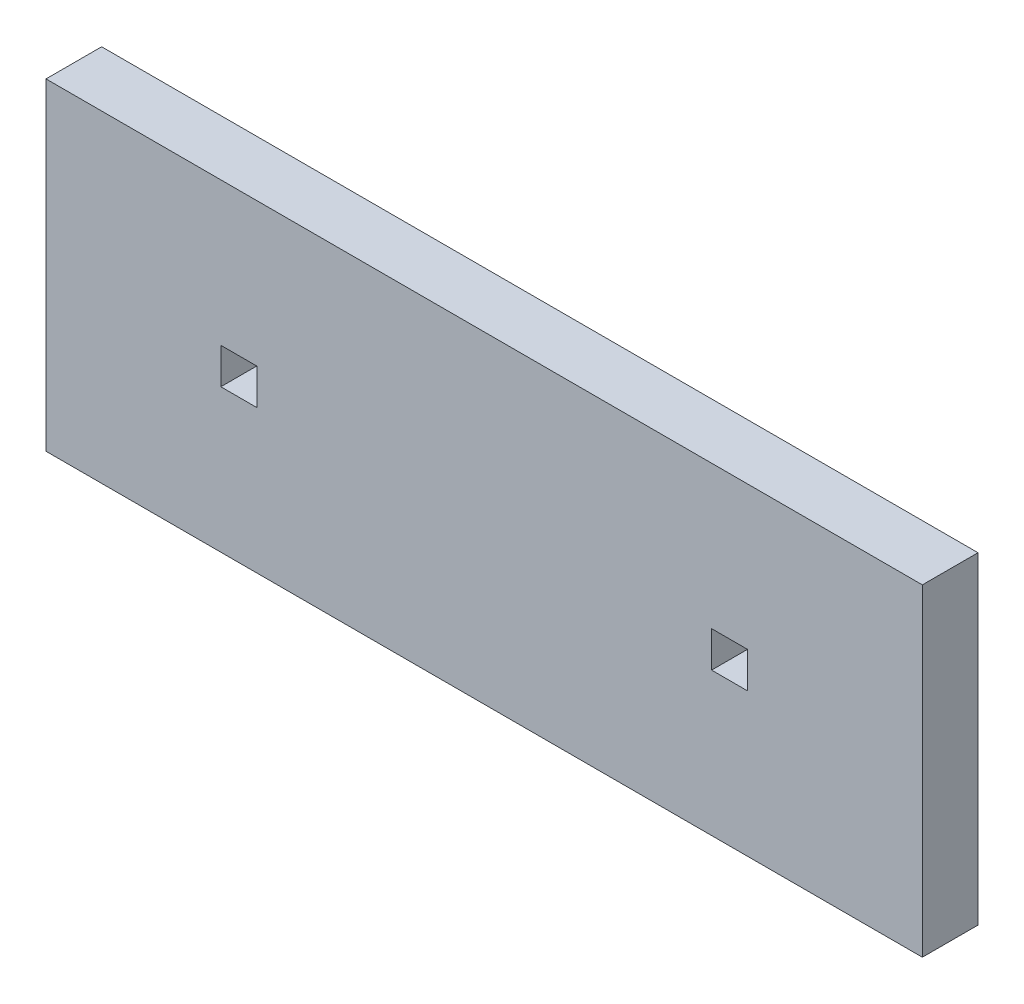
SolidWorks part; units mm, degrees
material "Acrylic (Medium-high impact)"
ref_plane "Front Plane" through (0, 0, 0) normal (0, 0, 1) x (1, 0, 0)
ref_plane "Top Plane" through (0, 0, 0) normal (0, 1, 0) x (1, 0, 0)
ref_plane "Right Plane" through (0, 0, 0) normal (1, 0, 0) x (0, 0, -1)
sketch "Sketch2" plane through (0, 0, 0) normal (0, 0, 1) x (1, 0, 0)
  line L0 (-12.975, -1.5875) -> (12.975, -1.5875) construction
  line L1 (25, -10.7875) -> (-25, -10.7875)
  line L2 (25, -10.7875) -> (25, 10.7875)
  line L3 (25, 10.7875) -> (-25, 10.7875)
  line L4 (-25, -10.7875) -> (-25, 10.7875)
  line L5 (25, -10.7875) -> (-25, 10.7875) construction
  line L6 (25, 10.7875) -> (-25, -10.7875) construction
  line L7 (-15.025, -0.5625) -> (-12.975, -0.5625)
  line L8 (-15.025, -0.5625) -> (-15.025, -2.6125)
  line L9 (-15.025, -2.6125) -> (-12.975, -2.6125)
  line L10 (-12.975, -0.5625) -> (-12.975, -2.6125)
  line L11 (15.025, -2.6125) -> (12.975, -2.6125)
  line L12 (15.025, -2.6125) -> (15.025, -0.5625)
  line L13 (15.025, -0.5625) -> (12.975, -0.5625)
  line L14 (12.975, -2.6125) -> (12.975, -0.5625)
  line L15 (-18, 10.7875) -> (-18, -10.7875) construction
  line L16 (0, -1.6485) -> (0, 1.6485) construction
  line L17 (22.5, 10.7875) -> (20.5, 10.7875)
  line L22 (-25, 10.7875) -> (-18, 10.7875)
  line L23 (-25, 10.7875) -> (-25, 7.6125)
  line L24 (-25, 7.6125) -> (-18, 7.6125)
  line L25 (-18, 10.7875) -> (-18, 7.6125)
  line L26 (-22.5, 7.6125) -> (-20.5, 7.6125)
  line L27 (-22.5, 7.6125) -> (-22.5, 10.7875)
  line L28 (-22.5, 10.7875) -> (-20.5, 10.7875)
  line L29 (-20.5, 7.6125) -> (-20.5, 10.7875)
  line L30 (20.5, 7.6125) -> (20.5, 10.7875)
  line L31 (22.5, 7.6125) -> (20.5, 7.6125)
  line L32 (22.5, 7.6125) -> (22.5, 10.7875)
  line L33 (25, 7.6125) -> (18, 7.6125)
  line L34 (18, 10.7875) -> (18, 7.6125)
  line L35 (25, 10.7875) -> (18, 10.7875)
  line L36 (25, 10.7875) -> (25, 7.6125)
  line L42 (-18, 10.7875) -> (18, 10.7875)
  line L43 (-18, 10.7875) -> (-18, 7.6125)
  line L44 (-18, 7.6125) -> (18, 7.6125)
  line L45 (18, 10.7875) -> (18, 7.6125)
  line L46 (-25, -1) -> (-28.175, -1)
  line L47 (-25, -1) -> (-25, 1)
  line L48 (-25, 1) -> (-28.175, 1)
  line L49 (-28.175, -1) -> (-28.175, 1)
  line L50 (25, -1) -> (28.175, -1)
  line L51 (25, -1) -> (25, 1)
  line L52 (25, 1) -> (28.175, 1)
  line L53 (28.175, -1) -> (28.175, 1)
  point P0 (0, 0)
  point P16 (0, -1.5875)
  point P29 (-21.5, 7.6125)
  point P30 (-21.5, 7.6125)
  point P32 (-22.5, 9.2)
  point P40 (-14, -0.5625)
  point P41 (14, -0.5625)
  point P42 (-15.025, -1.5875)
  point P49 (28.175, 0)
  point P50 (-28.175, 0)
  dimension "D1" = 2.05
  dimension "D3" = 50
  dimension "D6" = 7
  dimension "D7" = 2
  dimension "D8" = 3.175
  dimension "D4" = 28
  dimension "D5" = 9.2
  dimension "D9" = 2
  dimension "D10" = 3.175
  dimension "D2" = 18.4
extrude "Boss-Extrude1" add sketch "Sketch2" along normal blind 3.175 contours L34 L3 L25 L24 L4 L1 L2 L33 L31 L7 L10 L9 L8 L11 L14 L13 L12
sketch "Sketch3" plane through (0, 0, 3.175) normal (0, 0, 1) x (1, 0, 0)
  line L0 (-25, 7.6125) -> (25, 7.6125) construction
  line L1 (-14.95, 7.6125) -> (14.95, 7.6125)
  line L2 (-14.95, 7.6125) -> (-14.95, 3.654)
  line L3 (-14.95, 3.654) -> (14.95, 3.654)
  line L4 (14.95, 7.6125) -> (14.95, 3.654)
  line L5 (0, 3.654) -> (0, 0) construction
  dimension "D1" = 29.9
  dimension "D2" = 3.9585
extrude "Cut-Extrude1" [suppressed] cut sketch "Sketch3" against normal through all
equation "\"bottomThickness\"= .220in"
equation "\"wallThickness\"= .125in"
equation "\"D10@Sketch2\"=\"wallThickness\""
equation "\"D8@Sketch2\"=\"wallThickness\""
equation "\"D1@Boss-Extrude1\"=\"wallThickness\""
